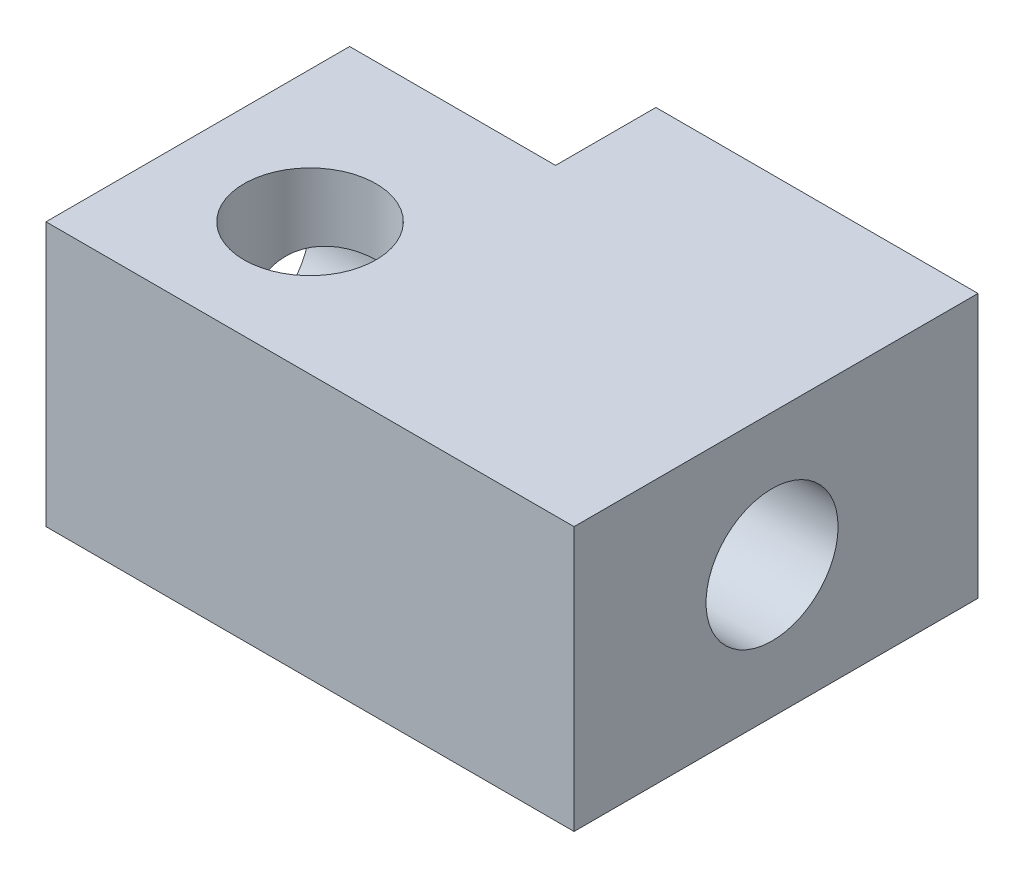
SolidWorks part; units mm, degrees
ref_plane "Front Plane" through (0, 0, 0) normal (0, 0, 1) x (1, 0, 0)
ref_plane "Top Plane" through (0, 0, 0) normal (0, 1, 0) x (1, 0, 0)
ref_plane "Right Plane" through (0, 0, 0) normal (1, 0, 0) x (0, 0, -1)
sketch "Sketch4" plane through (0, 0, 0) normal (0, 1, 0) x (1, 0, 0)
  line L0 (5, -5) -> (5, -86)
  line L5 (5, -86) -> (79, -86)
  line L6 (81.5, -5) -> (81.5, -82.25)
  line L7 (5, -5) -> (81.5, -5)
  line L8 (5, -5) -> (81.5, -5) construction
  line L9 (5, -5) -> (5, -86) construction
  line L10 (-7.25, -5) -> (-7.25, -86)
  line L11 (91.25, -5) -> (91.25, -88.5)
  line L12 (79, -5) -> (79, -88.5)
  line L13 (79, -82.75) -> (82.9, -82.75)
  line L14 (82.9, -5) -> (82.9, -82.75)
  line L16 (5, -88.5) -> (89, -88.5)
  line L18 (82.9, -80.85) -> (89, -80.85)
  line L20 (91.25, -5) -> (91.25, -86) construction
  line L21 (82.9, -5) -> (82.9, -86) construction
  line L22 (81.5, -5) -> (81.5, -86) construction
  line L24 (81.5, -5) -> (81.5, -86) construction
  line L26 (89, -80.85) -> (89, -88.5)
  circle A0 centre (5, -5) radius 1.25
  circle A1 centre (81.5, -5) radius 1.25
  circle A2 centre (81.5, -86) radius 1.25
  circle A3 centre (5, -86) radius 1.25
  point P19 (5, -83.5)
  point P21 (81.5, -83.5)
  point P23 (79, -83.5)
  point P24 (91.25, -83.5)
  point P28 (79, -82.1)
  point P29 (91.25, -82.1)
  point P32 (88.5, -5)
  point P35 (88.5, -88.5)
  point P40 (79, -82.25)
  point P41 (82.9, -82.25)
  dimension "D1" = 2
  dimension "D3" = 76.5
  dimension "D4" = 81
  dimension "D7" = 1.4
  dimension "D5" = 12.25
  dimension "D6" = 9.75
  dimension "D2" = 2
extrude "Boss-Extrude2" add sketch "Sketch4" along normal blind 5
sketch "Sketch5" plane through (89, 0, 0) normal (1, 0, 0) x (0, 0, -1)
  line L0 (-88.5, 0) -> (-88.5, 5)
  line L1 (-84.75, 0) -> (-84.75, 5)
  circle A1 centre (-84.75, 2.5) radius 1.25
  dimension "D1" = 3.75
extrude "Cut-Extrude2" cut sketch "Sketch5" against normal blind 10 contours L1 A1 | L1 A1
